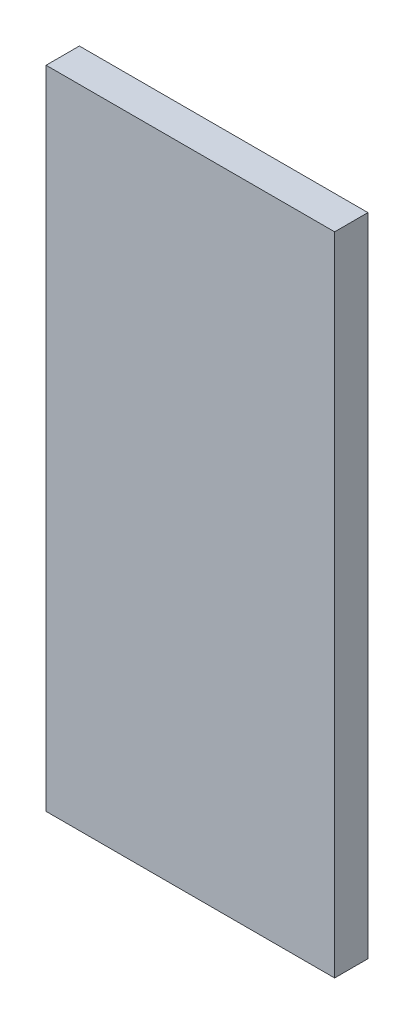
SolidWorks part; units mm, degrees
ref_plane "Front Plane" through (0, 0, 0) normal (0, 0, 1) x (1, 0, 0)
ref_plane "Top Plane" through (0, 0, 0) normal (0, 1, 0) x (1, 0, 0)
ref_plane "Right Plane" through (0, 0, 0) normal (1, 0, 0) x (0, 0, -1)
sketch "Sketch1" plane through (0, 0, 0) normal (0, 0, 1) x (1, 0, 0)
  line L0 (-13.2548, 13) -> (66, 13) construction
  line L1 (63.9411, 13) -> (-22.7426, 13)
  line L2 (63.9411, 13) -> (63.9411, -181.1389)
  line L3 (63.9411, -181.1389) -> (-22.7426, -181.1389)
  line L4 (-22.7426, 13) -> (-22.7426, -181.1389)
extrude "Boss-Extrude2" add sketch "Sketch1" along normal blind 10
